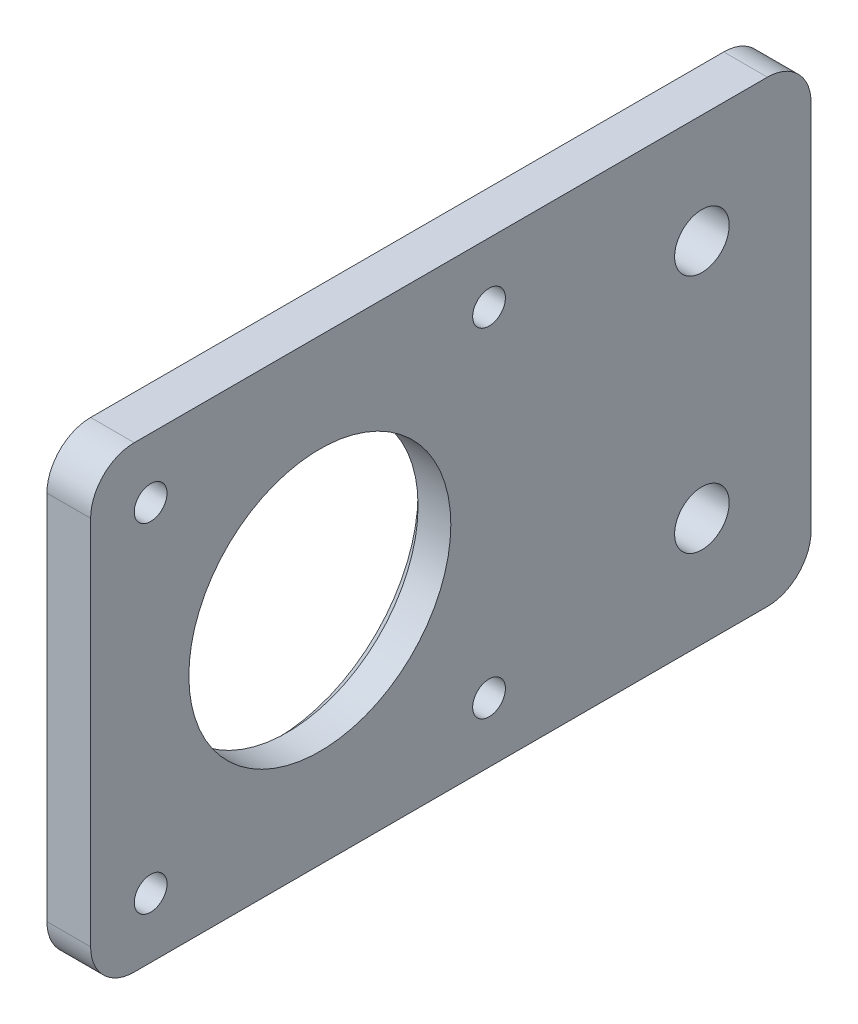
SolidWorks part; units mm, degrees
ref_plane "Front Plane" through (0, 0, 0) normal (0, 0, 1) x (1, 0, 0)
ref_plane "Top Plane" through (0, 0, 0) normal (0, 1, 0) x (1, 0, 0)
ref_plane "Right Plane" through (0, 0, 0) normal (1, 0, 0) x (0, 0, -1)
sketch "Sketch1" plane through (0, 0, 0) normal (0, 1, 0) x (1, 0, 0)
  line L0 (0, 0) -> (0, 42)
  line L1 (0, -55) -> (0, 55) construction
  line L2 (0, 42) -> (-20, 42)
  line L3 (-20, 42) -> (-20, 46)
  line L4 (-20, 46) -> (4, 46)
  line L5 (4, 46) -> (4, 0)
  line L6 (-55, 0) -> (55, 0) construction
  line L7 (4, 0) -> (0, 0)
extrude "Boss-Extrude1" add sketch "Sketch1" along normal blind 42
sketch "Sketch2" plane through (0, 0, 0) normal (-1, 0, 0) x (0, 0, 1)
  line L0 (-42, 21) -> (0, 21) construction
  line L1 (-42, 42) -> (-42, 0) construction
  line L2 (0, 21) -> (-21, 0) construction
  line L3 (-42, 0) -> (0, 0) construction
  line L4 (-21, 0) -> (-21, 5.5) construction
  line L5 (-42, 42) -> (0, 42) construction
  line L7 (-35, 5.5) -> (-36.5, 5.5)
  line L8 (-21, 21) -> (-21, 42) construction
  circle A0 centre (-21, 21) radius 12
  circle A1 centre (-36.5, 5.5) radius 1.5
  circle A2 centre (-5.5, 5.5) radius 1.5
  circle A3 centre (-5.5, 36.5) radius 1.5
  circle A4 centre (-36.5, 36.5) radius 1.5
  dimension "D1" = 15.5
  dimension "D2" = 24
extrude "Cut-Extrude1" cut sketch "Sketch2" against normal through all contours A0 | A4 | A3 | A2 | A1
sketch "Sketch3" plane through (0, 0, -42) normal (0, 0, 1) x (1, 0, 0)
  line L0 (-10, 0) -> (-10, 42) construction
  line L1 (-20, 0) -> (0, 0) construction
  line L2 (-20, 42) -> (0, 42) construction
  line L3 (-10, 42) -> (-10, 32) construction
  line L4 (-10, 21) -> (-20, 21) construction
  line L5 (-20, 42) -> (-20, 0) construction
  circle A0 centre (-10, 32) radius 2
  circle A1 centre (-10, 10) radius 2
extrude "Cut-Extrude2" cut sketch "Sketch3" against normal through all contours A0 | A1
chamfer "Chamfer1" distance 2 angle 45 2 edges at (-8, 32, -42) (-8, 10, -42)
chamfer "Chamfer2" distance 1 angle 45 1 edges at (0, 21, -9)
fillet "Fillet1" radius 4 5 edges at (4, 21, -46) (2, 0, 0) (2, 42, 0) (-20, 0, -44) (-20, 42, -44)
sketch "Sketch4" plane through (0, 0, 0) normal (0, -1, 0) x (1, 0, 0)
  line L0 (0, -42) -> (0, -46) construction
  line L1 (0, -46) -> (0, -66)
  line L2 (0, -66) -> (4, -66)
  line L3 (4, -66) -> (4, -42)
  line L4 (4, -42) -> (0, -42)
  line L5 (0, -42) -> (0, -46)
extrude "Boss-Extrude2" add sketch "Sketch4" against normal up to vertex (42 mm away)
sketch "Sketch5" plane through (0, 42, 0) normal (0, 1, 0) x (1, 0, 0)
  line L0 (0, 46) -> (0, 42)
  line L1 (0, 42) -> (-27.1686, 42)
  line L2 (-27.1686, 42) -> (-27.1686, 46)
  line L3 (-27.1686, 46) -> (0, 46)
extrude "Cut-Extrude3" cut sketch "Sketch5" against normal blind 44
sketch "Sketch6" plane through (0, 0, 0) normal (-1, 0, 0) x (0, 0, 1)
  line L0 (-66, 42) -> (-56, 42) construction
  line L1 (-66, 42) -> (-4, 42) construction
  line L2 (-56, 42) -> (-56, 32) construction
  line L3 (-66, 21) -> (-60.1002, 21) construction
  line L4 (-66, 42) -> (-66, 0) construction
  circle A0 centre (-56, 32) radius 2.5
  circle A1 centre (-56, 10) radius 2.5
extrude "Cut-Extrude4" cut sketch "Sketch6" against normal blind 44
fillet "Fillet2" radius 4 2 edges at (2, 0, -66) (2, 42, -66)
